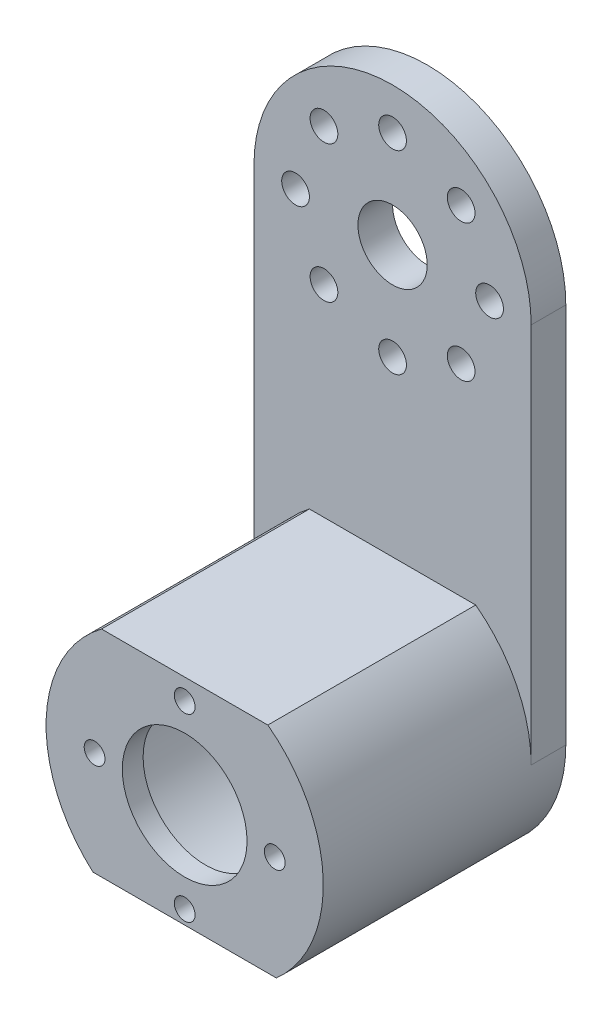
SolidWorks part; units mm, degrees
ref_plane "Plan de face" through (0, 0, 0) normal (0, 0, 1) x (1, 0, 0)
ref_plane "Plan de dessus" through (0, 0, 0) normal (0, 1, 0) x (1, 0, 0)
ref_plane "Plan de droite" through (0, 0, 0) normal (1, 0, 0) x (0, 0, -1)
sketch "Esquisse1" plane through (0, 0, 0) normal (0, 0, 1) x (1, 0, 0)
  line L1 (20, -20) -> (20, -75)
  line L3 (0, 0) -> (0, 23.2042) construction
  line L4 (-20, -20) -> (-20, -75)
  arc A0 (-20, -75) -> (20, -75) centre (0, -75) ccw
  arc A1 (20, -20) -> (-20, -20) centre (0, -20) ccw
  circle A2 centre (0, -75) radius 15
  circle A3 centre (0, -20) radius 5
  circle A4 centre (-14, -20) radius 2
  circle A5 centre (-9.8995, -10.1005) radius 2
  circle A6 centre (0, -6) radius 2
  circle A7 centre (9.8995, -10.1005) radius 2
  circle A8 centre (14, -20) radius 2
  circle A9 centre (9.8995, -29.8995) radius 2
  circle A10 centre (0, -34) radius 2
  circle A11 centre (-9.8995, -29.8995) radius 2
  dimension "D1" = 30
extrude "Extrusion1" add sketch "Esquisse1" along normal blind 5
sketch "Esquisse2" plane through (0, 0, 5) normal (0, 0, 1) x (1, 0, 0)
  line L1 (12, -59) -> (-12, -59)
  arc A0 (-12, -59) -> (12, -59) centre (0, -75) ccw
  circle A1 centre (0, -75) radius 9
  circle A3 centre (0, -62) radius 1.5
  circle A4 centre (0, -88) radius 1.5
  circle A5 centre (-13, -75) radius 1.5
  circle A6 centre (13, -75) radius 1.5
extrude "Extrusion2" add sketch "Esquisse2" along normal blind 30
sketch "Esquisse3" plane through (0, 0, 5) normal (0, 0, -1) x (-1, 0, 0)
  circle A0 centre (0, -75) radius 15
extrude "Extrusion3" cut sketch "Esquisse3" against normal blind 27
sketch "Esquisse4" plane through (0, 0, 0) normal (1, 0, 0) x (0, 0, -1)
  line L0 (-35, -95) -> (-30, -95)
  line L1 (-35, -95) -> (0, -95) construction
  line L2 (-35, -95) -> (-35, -90)
  line L3 (-35, -59) -> (-35, -95) construction
  line L4 (-35, -90) -> (-30, -95)
extrude "Extrusion4" cut sketch "Esquisse4" against normal through all and the other way through all
